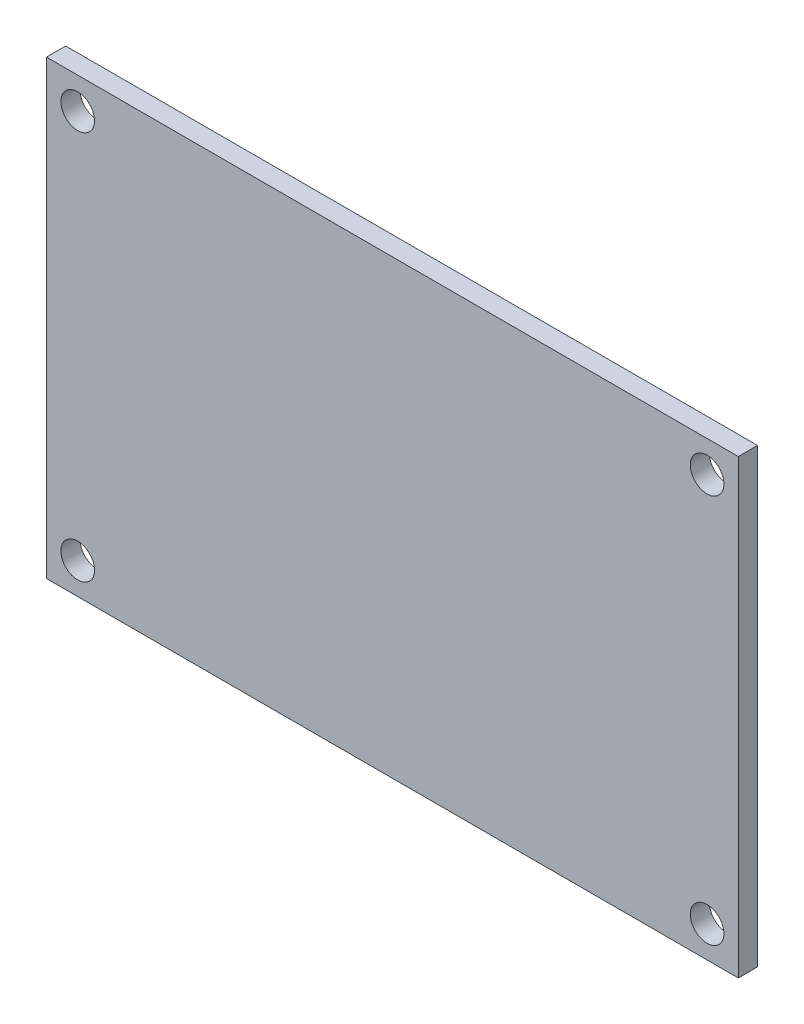
SolidWorks part; units mm, degrees
ref_plane "Płaszczyzna przednia" through (0, 0, 0) normal (0, 0, 1) x (1, 0, 0)
ref_plane "Płaszczyzna górna" through (0, 0, 0) normal (0, 1, 0) x (1, 0, 0)
ref_plane "Płaszczyzna prawa" through (0, 0, 0) normal (1, 0, 0) x (0, 0, -1)
sketch "Sketch1" plane through (0, 0, 0) normal (0, 0, 1) x (1, 0, 0)
  line L1 (-36, -23.5) -> (36, -23.5)
  line L2 (-36, -23.5) -> (-36, 23.5)
  line L3 (-36, 23.5) -> (36, 23.5)
  line L4 (36, -23.5) -> (36, 23.5)
  line L5 (-36, -23.5) -> (36, 23.5) construction
  line L6 (-36, 23.5) -> (36, -23.5) construction
  point P0 (0, 0)
  dimension "D1" = 72
  dimension "D2" = 47
extrude "Boss-Extrude1" add sketch "Sketch1" along normal blind 2
sketch "Sketch2" plane through (0, 0, 0) normal (0, 0, 1) x (1, 0, 0)
  line L1 (32.75, -20.25) -> (-32.75, -20.25) construction
  line L2 (32.75, -20.25) -> (32.75, 20.25) construction
  line L3 (32.75, 20.25) -> (-32.75, 20.25) construction
  line L4 (-32.75, -20.25) -> (-32.75, 20.25) construction
  line L5 (32.75, -20.25) -> (-32.75, 20.25) construction
  line L6 (32.75, 20.25) -> (-32.75, -20.25) construction
  circle A0 centre (-32.75, 20.25) radius 1.75
  circle A1 centre (32.75, 20.25) radius 1.75
  circle A2 centre (32.75, -20.25) radius 1.75
  circle A3 centre (-32.75, -20.25) radius 1.75
  point P0 (0, 0)
  dimension "D3" = 3.5
  dimension "D4" = 3.5
  dimension "D5" = 3.5
  dimension "D6" = 3.5
  dimension "D1" = 65.5
  dimension "D2" = 40.5
extrude "Cut-Extrude1" cut sketch "Sketch2" along normal through all both and the other way through all
